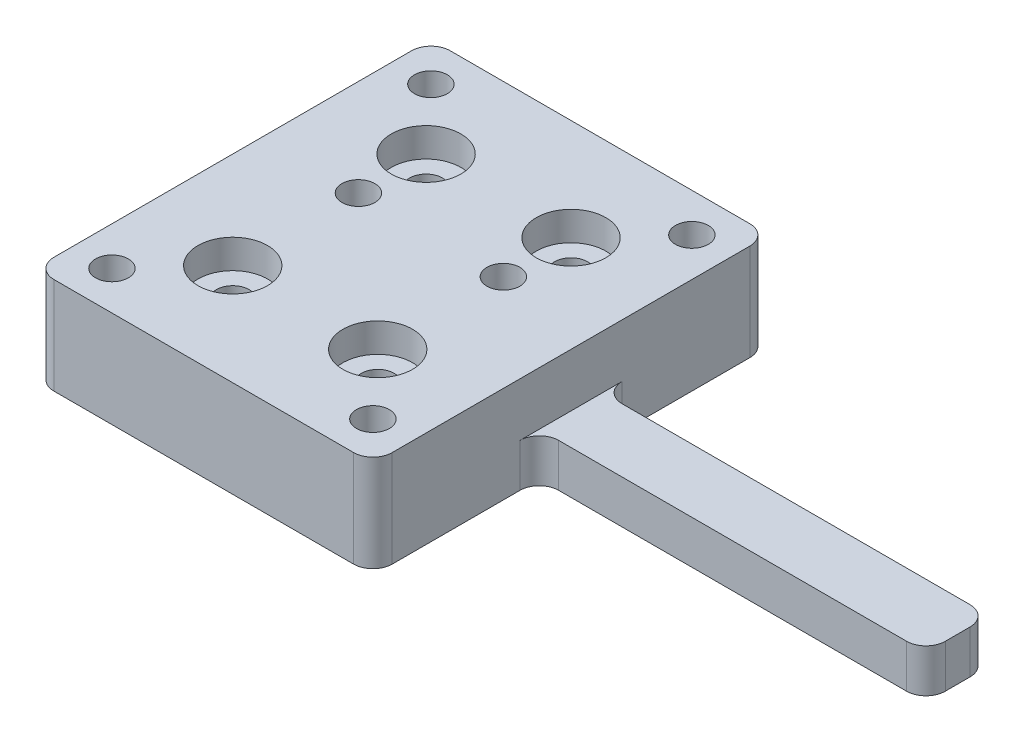
SolidWorks part; units mm, degrees
ref_plane "前视基准面" through (0, 0, 0) normal (0, 0, 1) x (1, 0, 0)
ref_plane "上视基准面" through (0, 0, 0) normal (0, 1, 0) x (1, 0, 0)
ref_plane "右视基准面" through (0, 0, 0) normal (1, 0, 0) x (0, 0, -1)
sketch "草图1" plane through (0, 0, 0) normal (0, 1, 0) x (1, 0, 0)
  line L0 (-1.7143, 4.8571) -> (-36.7143, 4.8571) construction
  line L1 (-36.7143, 25.3571) -> (-1.7143, 25.3571)
  line L2 (-36.7143, 25.3571) -> (-36.7143, -15.6429)
  line L3 (-36.7143, -15.6429) -> (-1.7143, -15.6429)
  line L4 (-1.7143, 25.3571) -> (-1.7143, -15.6429)
  line L5 (-36.7143, 14.8571) -> (-1.7143, 14.8571) construction
  line L6 (-36.7143, -5.1429) -> (-1.7143, -5.1429) construction
  line L7 (-19.2143, 25.3571) -> (-19.2143, -15.6429) construction
  line L8 (-1.7143, 7.8571) -> (-36.7143, 7.8571) construction
  circle A0 centre (-26.7143, 14.8571) radius 1.7
  circle A1 centre (-11.7143, 14.8571) radius 1.7
  circle A2 centre (-11.7143, -5.1429) radius 1.7
  circle A3 centre (-26.7143, -5.1429) radius 1.7
  circle A4 centre (-11.7143, 7.8571) radius 1.7
  circle A5 centre (-26.7143, 7.8571) radius 1.7
  dimension "D6" = 3.4
  dimension "D1" = 41
  dimension "D2" = 35
  dimension "D3" = 10
  dimension "D4" = 10
  dimension "D5" = 7.5
  dimension "D7" = 7
extrude "凸台-拉伸1" add sketch "草图1" along normal blind 10
sketch "草图2" plane through (0, 10, 0) normal (0, 1, 0) x (1, 0, 0)
  circle A0 centre (-26.7143, -5.1429) radius 3.6
  circle A1 centre (-11.7143, -5.1429) radius 3.6
  circle A2 centre (-11.7143, 14.8571) radius 3.6
  circle A3 centre (-26.7143, 14.8571) radius 3.6
extrude "切除-拉伸1" cut sketch "草图2" against normal blind 3
sketch "草图3" plane through (0, 0, 0) normal (0, -1, 0) x (1, 0, 0)
  circle A0 centre (-11.7143, -7.8571) radius 3.4
  circle A1 centre (-26.7143, -7.8571) radius 3.4
extrude "切除-拉伸2" cut sketch "草图3" against normal blind 5
sketch "草图4" plane through (0, 10, 0) normal (0, 1, 0) x (1, 0, 0)
  line L0 (-19.2143, 25.3571) -> (-19.2143, -15.6429) construction
  line L1 (-1.7143, 25.3571) -> (-36.7143, 25.3571) construction
  line L2 (-36.7143, -15.6429) -> (-1.7143, -15.6429) construction
  line L3 (-1.7143, 4.8571) -> (-36.7143, 4.8571) construction
  line L4 (-1.7143, -15.6429) -> (-1.7143, 25.3571) construction
  line L5 (-36.7143, 25.3571) -> (-36.7143, -15.6429) construction
  circle A0 centre (-32.7143, 21.3571) radius 1.7
  circle A1 centre (-5.7143, 21.3571) radius 1.7
  circle A2 centre (-5.7143, -11.6429) radius 1.7
  circle A3 centre (-32.7143, -11.6429) radius 1.7
  point P16 (-36.7143, 16.1446)
  dimension "D1" = 4
  dimension "D3" = 3.4
  dimension "D2" = 4
  dimension "D4" = 16.5
extrude "切除-拉伸3" cut sketch "草图4" against normal through all
fillet "圆角1" radius 2 4 edges at (-1.7143, 5, -25.3571) (-36.7143, 5, -25.3571) (-36.7143, 5, 15.6429) (-1.7143, 5, 15.6429)
sketch "草图5" plane through (-1.7143, 0, 0) normal (1, 0, 0) x (0, 0, -1)
  line L0 (4.8571, 0) -> (4.8571, 10) construction
  line L1 (-13.6429, 0) -> (23.3571, 0) construction
  line L2 (-13.6429, 10) -> (23.3571, 10) construction
  line L4 (1.5759, 4.4787) -> (8.1384, 4.4787)
  line L5 (1.5759, 4.4787) -> (1.5759, 0)
  line L6 (1.5759, 0) -> (8.1384, 0)
  line L7 (8.1384, 4.4787) -> (8.1384, 0)
  line L8 (1.5759, 4.4787) -> (8.1384, 0) construction
  line L9 (1.5759, 0) -> (8.1384, 4.4787) construction
  point P6 (4.8571, 2.2394)
extrude "凸台-拉伸2" add sketch "草图5" along normal blind 40
fillet "圆角2" radius 2 4 edges at (-1.7143, 2.2394, -8.1384) (-1.7143, 2.2394, -1.5759) (38.2857, 2.2394, -8.1384) (38.2857, 2.2394, -1.5759)
